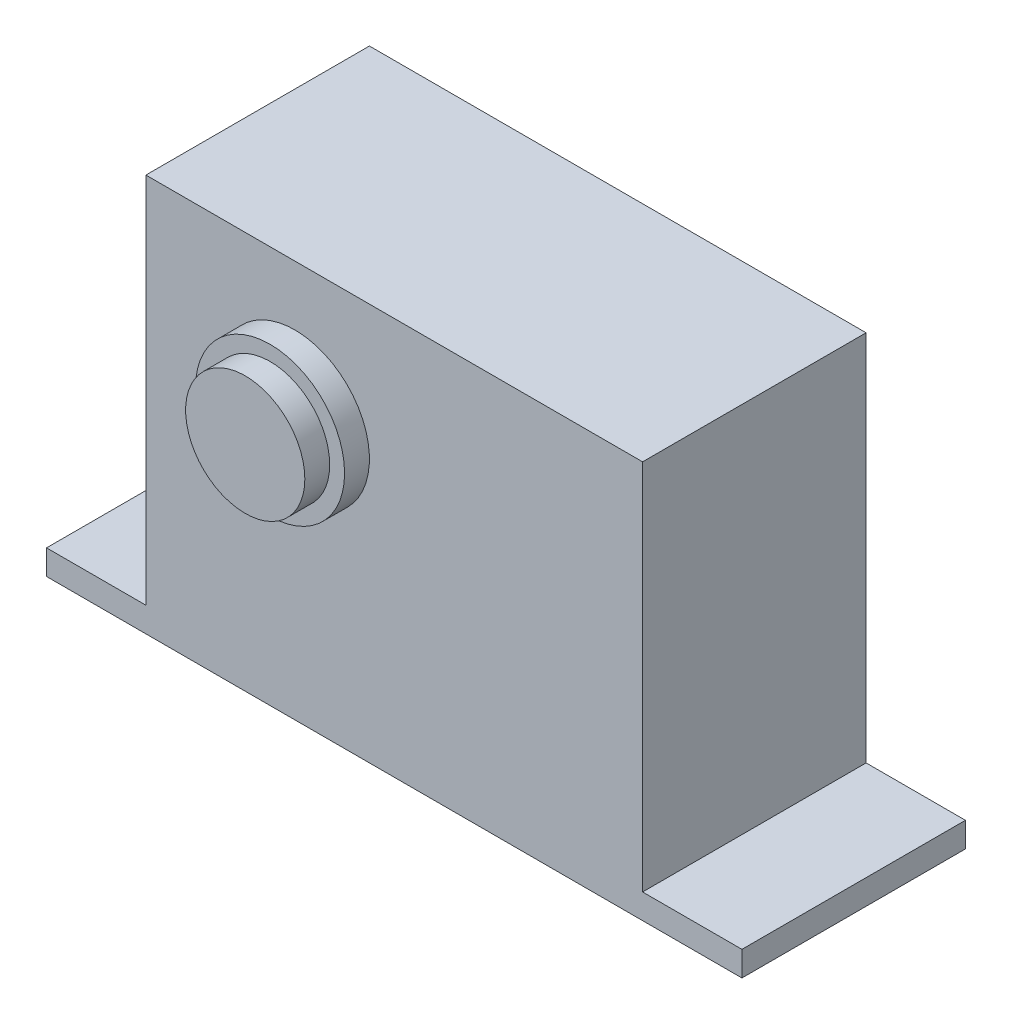
SolidWorks part; units mm, degrees
ref_plane "Front Plane" through (0, 0, 0) normal (0, 0, 1) x (1, 0, 0)
ref_plane "Top Plane" through (0, 0, 0) normal (0, 1, 0) x (1, 0, 0)
ref_plane "Right Plane" through (0, 0, 0) normal (1, 0, 0) x (0, 0, -1)
sketch "Sketch1" plane through (0, 0, 0) normal (0, 0, 1) x (1, 0, 0)
  line L1 (0, 0) -> (70, 0)
  line L2 (0, 0) -> (0, 40)
  line L3 (0, 40) -> (70, 40)
  line L4 (70, 0) -> (70, 40)
  dimension "D1" = 40
  dimension "D2" = 70
extrude "Boss-Extrude1" add sketch "Sketch1" along normal blind 22.5
sketch "Sketch2" plane through (0, 0, 22.5) normal (0, 0, 1) x (1, 0, 0)
  line L0 (0, 0) -> (70, 0) construction
  line L1 (70, 0) -> (70, 40) construction
  circle A0 centre (25, 26.5) radius 7.5
  dimension "D1" = 26.5
  dimension "D3" = 15
  dimension "D2" = 45
extrude "Boss-Extrude2" add sketch "Sketch2" along normal blind 2.5
sketch "Sketch3" plane through (0, 0, 25) normal (0, 0, 1) x (1, 0, 0)
  circle A0 centre (25, 26.5) radius 6
  dimension "D1" = 12
extrude "Boss-Extrude3" add sketch "Sketch3" along normal blind 2.5
sketch "Sketch4" plane through (0, 0, 0) normal (-1, 0, 0) x (0, 0, 1)
  line L0 (22.5, 40) -> (22.5, 0) construction
  line L1 (0, 2.5) -> (0, 40)
  line L2 (0, 40) -> (22.5, 40)
  line L3 (0, 2.5) -> (22.5, 2.5)
  line L4 (22.5, 40) -> (22.5, 2.5)
  line L5 (22.5, 0) -> (0, 0) construction
  dimension "D1" = 2.5
extrude "Cut-Extrude1" cut sketch "Sketch4" against normal blind 10
sketch "Sketch5" plane through (70, 0, 0) normal (1, 0, 0) x (0, 0, -1)
  line L0 (-22.5, 2.5) -> (-22.5, 40) construction
  line L1 (0, 40) -> (0, 2.5) construction
  line L2 (-22.5, 40) -> (0, 40) construction
  line L3 (0, 2.5) -> (-22.5, 2.5) construction
  line L4 (-22.5, 2.5) -> (-22.5, 40)
  line L5 (0, 40) -> (0, 2.5)
  line L6 (-22.5, 40) -> (0, 40)
  line L7 (0, 2.5) -> (-22.5, 2.5)
extrude "Cut-Extrude2" cut sketch "Sketch5" against normal blind 10
